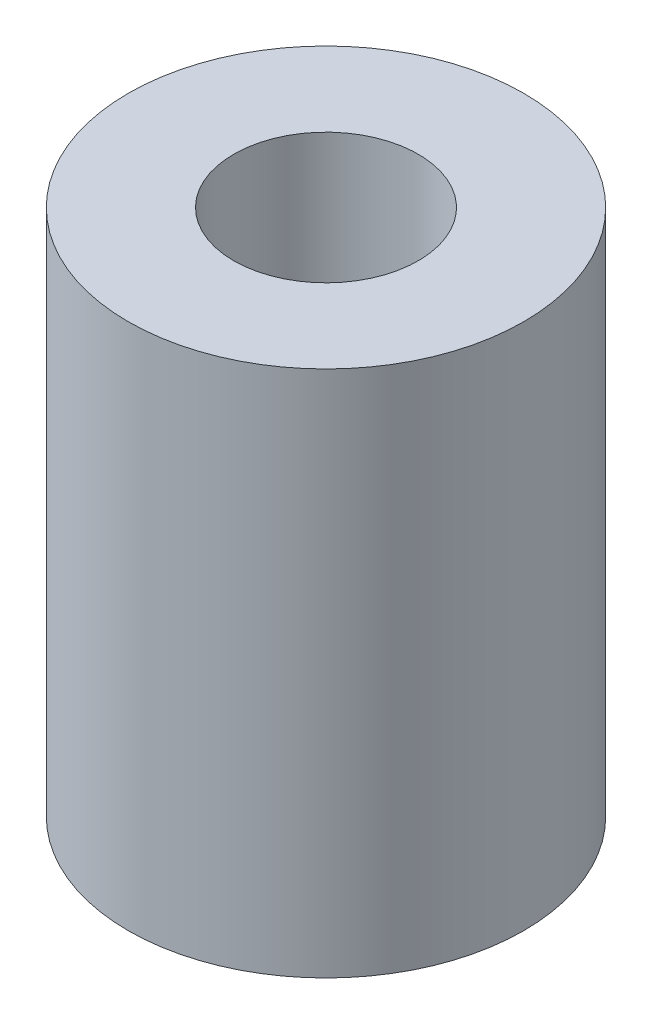
SolidWorks part; units mm, degrees
ref_plane "Front Plane" through (0, 0, 0) normal (0, 0, 1) x (1, 0, 0)
ref_plane "Top Plane" through (0, 0, 0) normal (0, 1, 0) x (1, 0, 0)
ref_plane "Right Plane" through (0, 0, 0) normal (1, 0, 0) x (0, 0, -1)
sketch "Sketch1" plane through (0, 0, 0) normal (0, 1, 0) x (1, 0, 0)
  circle A0 centre (0, 0) radius 3.75
  circle A1 centre (0, 0) radius 1.75
  dimension "D1" = 7.5
  dimension "D2" = 3.5
extrude "Boss-Extrude1" add sketch "Sketch1" along normal blind 10
